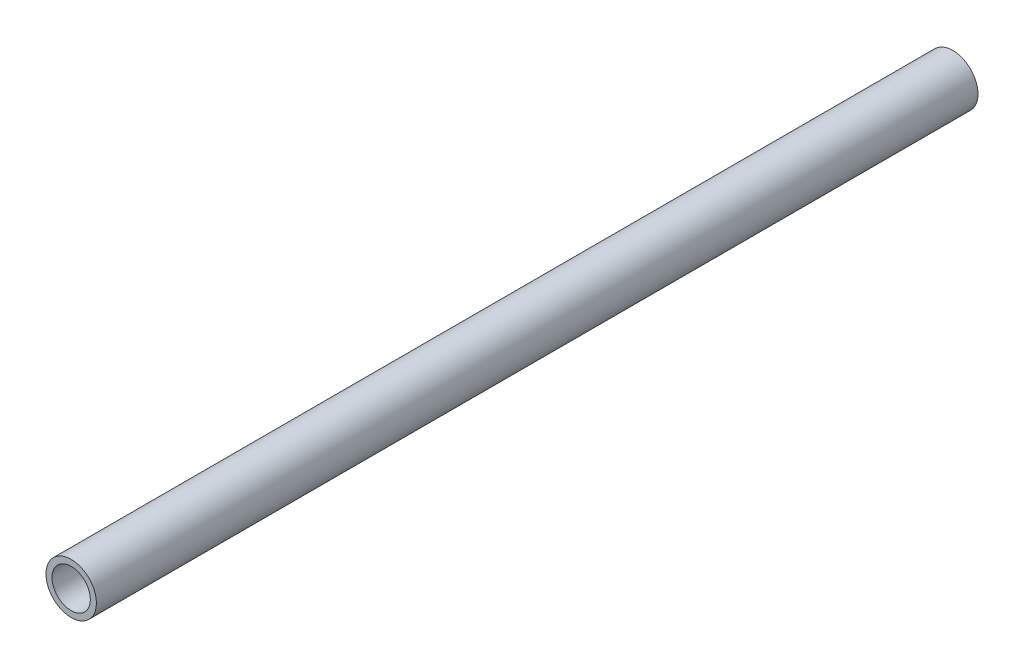
SolidWorks part; units mm, degrees
material "carbon"
ref_plane "Płaszczyzna XY" through (0, 0, 0) normal (0, 0, 1) x (1, 0, 0)
ref_plane "Płaszczyzna XZ" through (0, 0, 0) normal (0, 1, 0) x (1, 0, 0)
ref_plane "Płaszczyzna YZ" through (0, 0, 0) normal (1, 0, 0) x (0, 0, -1)
sketch "Szkic1" plane through (0, 0, 0) normal (0, 0, 1) x (1, 0, 0)
  circle A0 centre (0, 0) radius 6.35
  circle A1 centre (0, 0) radius 8.35
  dimension "D1" = 12.7
  dimension "D2" = 16.7
extrude "Dodanie-wyciągnięcie1" add sketch "Szkic1" along normal blind 266.7168 and the other way up to surface (25.2339 mm away)
